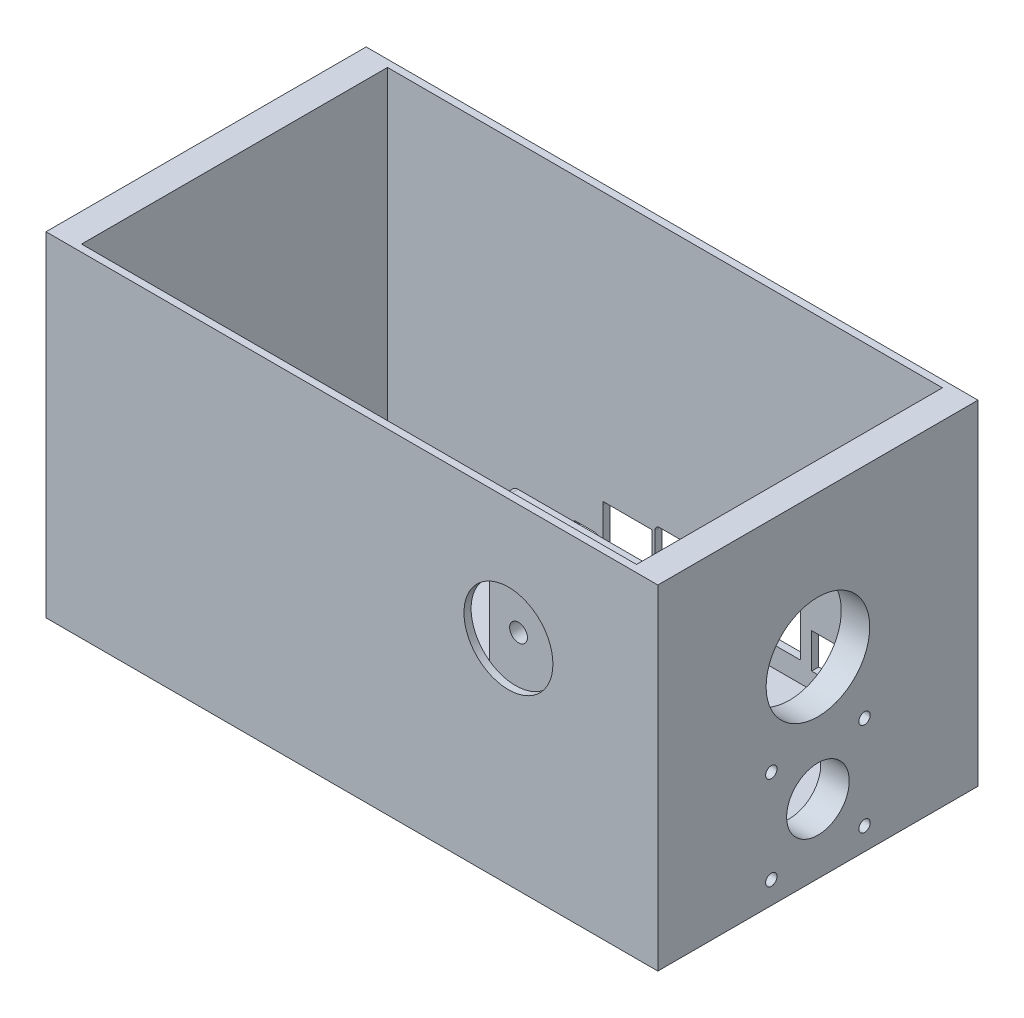
SolidWorks part; units mm, degrees
ref_plane "Front Plane" through (0, 0, 0) normal (0, 0, 1) x (1, 0, 0)
ref_plane "Top Plane" through (0, 0, 0) normal (0, 1, 0) x (1, 0, 0)
ref_plane "Right Plane" through (0, 0, 0) normal (1, 0, 0) x (0, 0, -1)
sketch "Sketch1" plane through (0, 0, 0) normal (0, 1, 0) x (1, 0, 0)
  line L1 (-101.6, -57.15) -> (101.6, -57.15)
  line L2 (-101.6, -57.15) -> (-101.6, 57.15)
  line L3 (-101.6, 57.15) -> (101.6, 57.15)
  line L4 (101.6, -57.15) -> (101.6, 57.15)
  line L5 (-101.6, -57.15) -> (101.6, 57.15) construction
  line L6 (-101.6, 57.15) -> (101.6, -57.15) construction
  point P0 (0, 0)
  dimension "10" = 203.2
  dimension "D2" = 114.3
extrude "Boss-Extrude1" add sketch "Sketch1" along normal blind 119.38
shell "Shell1" thickness 2.54
sketch "Sketch2" plane through (99.06, 0, 0) normal (-1, 0, 0) x (0, 0, 1)
  line L0 (22.225, 46.863) -> (-22.225, 46.863) construction
  line L5 (-22.225, 46.863) -> (-22.225, 2.413) construction
  line L10 (-22.225, 2.413) -> (22.225, 46.863) construction
  line L11 (-22.225, 46.863) -> (22.225, 2.413) construction
  line L12 (22.225, 46.863) -> (22.225, 2.413) construction
  line L14 (22.225, 2.413) -> (-22.225, 2.413) construction
  line L16 (0, 17.0459) -> (0, 33.3047) construction
  line L17 (1.822, 24.638) -> (-4.4847, 24.638) construction
  circle A0 centre (0, 68.58) radius 18.5
  circle A1 centre (16.637, 41.275) radius 2.032
  circle A5 centre (16.637, 8.001) radius 2.032
  circle A6 centre (-16.637, 8.001) radius 2.032
  circle A7 centre (-16.637, 41.275) radius 2.032
  circle A8 centre (0, 24.638) radius 11.176
  point P4 (0, 24.638)
  dimension "D3" = 37
  dimension "D4" = 4.064
  dimension "D5" = 33.274
  dimension "D6" = 22.352
  dimension "D1" = 44.45
  dimension "D2" = 44.45
extrude "Cut-Extrude1" cut sketch "Sketch2" against normal blind 2.54
sketch "Sketch3" plane through (101.6, 0, 0) normal (1, 0, 0) x (0, 0, -1)
  line L4 (-57.15, 0) -> (57.15, 0)
  line L5 (57.15, 0) -> (57.15, 119.38)
  line L6 (57.15, 119.38) -> (-57.15, 119.38)
  line L7 (-57.15, 119.38) -> (-57.15, 0)
  line L8 (-57.15, 0) -> (57.15, 0)
  line L9 (57.15, 0) -> (57.15, 119.38)
  line L10 (57.15, 119.38) -> (-57.15, 119.38)
  line L11 (-57.15, 119.38) -> (-57.15, 0)
  circle A0 centre (0, 68.58) radius 18.5 construction
  circle A1 centre (0, 68.58) radius 18.5
  circle A2 centre (-16.637, 8.001) radius 2.032 construction
  circle A3 centre (16.637, 8.001) radius 2.032 construction
  circle A4 centre (16.637, 41.275) radius 2.032 construction
  circle A5 centre (-16.637, 41.275) radius 2.032 construction
  circle A6 centre (-16.637, 8.001) radius 2.032
  circle A7 centre (16.637, 8.001) radius 2.032
  circle A8 centre (16.637, 41.275) radius 2.032
  circle A9 centre (-16.637, 41.275) radius 2.032
  circle A10 centre (0, 24.638) radius 11.176 construction
  circle A11 centre (0, 24.638) radius 11.176
  dimension "D1" = 0
extrude "Boss-Extrude3" add sketch "Sketch3" along normal blind 7.62
sketch "Sketch4" plane through (0, 0, 57.15) normal (0, 0, 1) x (1, 0, 0)
  line L1 (-101.6, 0) -> (109.22, 0) construction
  line L2 (109.22, 119.38) -> (109.22, 0) construction
  circle A0 centre (55.88, 76.2) radius 15.875
  dimension "D1" = 31.75
  dimension "D2" = 53.34
  dimension "D3" = 76.2
sketch "Sketch5" plane through (0, 2.54, 0) normal (0, 1, 0) x (1, 0, 0)
  line L5 (30.53, -38.55) -> (81.23, -38.55)
  line L6 (30.53, -38.55) -> (30.53, -30.93)
  line L7 (30.53, -30.93) -> (81.23, -30.93)
  line L8 (81.23, -38.55) -> (81.23, -30.93)
  line L9 (74.88, -38.55) -> (74.88, -39.95) construction
  dimension "D1" = 7.62
  dimension "D2" = 6.35
  dimension "D3" = 6.35
extrude "Cut-Extrude2" cut sketch "Sketch4" against normal blind 2.54
extrude "Boss-Extrude4" add sketch "Sketch5" along normal blind 95.25
sketch "Sketch6" plane through (0, 0, 38.55) normal (0, 0, 1) x (1, 0, 0)
  circle A1 centre (40.88, 91.2) radius 3.175
  circle A3 centre (70.88, 61.2) radius 3.175
  circle A4 centre (40.88, 61.2) radius 3.175
  circle A7 centre (70.88, 91.2) radius 3.175
  dimension "D1" = 6.35
  dimension "D2" = 6.35
  dimension "D3" = 6.35
  dimension "D4" = 6.35
extrude "Cut-Extrude3" cut sketch "Sketch6" against normal up to next
fillet "Fillet1" radius 2.54 2 edges at (30.53, 97.79, 34.74) (81.23, 97.79, 34.74)
fillet "Fillet2" radius 2.54 4 edges at (55.88, 2.54, 38.55) (81.23, 2.54, 34.74) (30.53, 2.54, 34.74) (55.88, 2.54, 30.93)
sketch "Sketch7" plane through (-101.6, 0, 0) normal (-1, 0, 0) x (0, 0, 1)
  line L4 (-57.15, 0) -> (57.15, 0)
  line L5 (57.15, 0) -> (57.15, 119.38)
  line L6 (57.15, 119.38) -> (-57.15, 119.38)
  line L7 (-57.15, 119.38) -> (-57.15, 0)
  line L8 (-57.15, 0) -> (57.15, 0)
  line L9 (57.15, 0) -> (57.15, 119.38)
  line L10 (57.15, 119.38) -> (-57.15, 119.38)
  line L11 (-57.15, 119.38) -> (-57.15, 0)
  dimension "D1" = 0
extrude "Boss-Extrude5" add sketch "Sketch7" along normal blind 7.62
sketch "Sketch8" plane through (0, 2.54, 0) normal (0, 1, 0) x (1, 0, 0)
  circle A2 centre (57.7271, -23.7315) radius 2.54
  circle A3 centre (59.6171, 34.2332) radius 2.54
  circle A4 centre (-26.2779, 34.2332) radius 2.54
  circle A5 centre (-28.2729, -23.7315) radius 2.54
  circle A6 centre (57.7271, -23.7315) radius 1.27
  circle A7 centre (59.6171, 34.2332) radius 1.27
  circle A8 centre (-26.2779, 34.2332) radius 1.27
  circle A9 centre (-28.2729, -23.7315) radius 1.27
  dimension "D1" = 5.08
  dimension "D2" = 5.08
  dimension "D3" = 5.08
  dimension "D4" = 5.08
  dimension "D5" = 2.54
  dimension "D6" = 2.54
  dimension "D7" = 2.54
  dimension "D8" = 2.54
extrude "Boss-Extrude6" add sketch "Sketch8" along normal blind 5.08
sketch "Sketch9" plane through (0, 0, -57.15) normal (0, 0, -1) x (-1, 0, 0)
  line L0 (-61.8671, 9.445) -> (-53.3671, 9.445) construction
  line L5 (-53.3671, 9.445) -> (-53.3671, 19.945) construction
  line L6 (-53.3671, 19.945) -> (-61.8671, 19.945) construction
  line L7 (-61.8671, 19.945) -> (-61.8671, 9.445) construction
  line L8 (-61.8671, 9.445) -> (-53.3671, 9.445) construction
  line L9 (-53.3671, 9.445) -> (-53.3671, 19.945) construction
  line L10 (-53.3671, 19.945) -> (-61.8671, 19.945) construction
  line L11 (-61.8671, 19.945) -> (-61.8671, 9.445) construction
  line L12 (-47.5171, 27.3712) -> (-32.2171, 27.3712)
  line L13 (-27.5671, 24.065) -> (-27.5671, 11.045) construction
  line L14 (-26.9671, 24.665) -> (-15.0671, 24.665) construction
  line L15 (-14.4671, 24.065) -> (-14.4671, 11.045) construction
  line L16 (-15.0671, 10.445) -> (-26.9671, 10.445) construction
  line L17 (-9.9671, 24.665) -> (1.9329, 24.665) construction
  line L18 (2.5329, 24.065) -> (2.5329, 11.045) construction
  line L19 (1.9329, 10.445) -> (-9.9671, 10.445) construction
  line L20 (-10.5671, 11.045) -> (-10.5671, 24.065) construction
  line L21 (-48.3171, 26.5712) -> (-48.3171, 10.1681)
  line L22 (-31.4234, 26.6712) -> (-31.4234, 10.107)
  line L23 (-48.0171, 9.8681) -> (-31.7171, 9.8681) construction
  line L24 (-48.0171, 9.8681) -> (-31.7171, 9.8681)
  line L25 (10.7029, 9.545) -> (15.7629, 9.545) construction
  line L26 (-62.8831, 8.429) -> (-52.3511, 8.429)
  line L27 (-52.3511, 8.429) -> (-52.3511, 20.961)
  line L28 (28.3629, 9.3212) -> (28.3629, 9.4912)
  line L29 (28.3629, 9.4912) -> (25.745, 9.4912)
  line L30 (25.5824, 9.5586) -> (24.9202, 10.2207)
  line L31 (24.8529, 10.3833) -> (24.8529, 11.2712)
  line L32 (25.0829, 11.5012) -> (31.6829, 11.5012)
  line L33 (31.9129, 11.2712) -> (31.9128, 10.3833)
  line L34 (31.8455, 10.2207) -> (31.1834, 9.5586)
  line L35 (31.0207, 9.4912) -> (28.4029, 9.4912)
  line L36 (28.4029, 9.4912) -> (28.4029, 9.3212)
  line L37 (28.4029, 9.3212) -> (31.0207, 9.3212)
  line L38 (31.3036, 9.4384) -> (31.9657, 10.1005)
  line L39 (32.0829, 10.3833) -> (32.0829, 11.2712)
  line L40 (31.6829, 11.6712) -> (25.0829, 11.6712)
  line L41 (24.6829, 11.2712) -> (24.6829, 10.3833)
  line L42 (24.8, 10.1005) -> (25.4621, 9.4384)
  line L43 (25.745, 9.3212) -> (28.3629, 9.3212)
  line L53 (28.4029, 9.3212) -> (31.0207, 9.3212) construction
  line L54 (31.3036, 9.4384) -> (31.9657, 10.1005) construction
  line L55 (32.0829, 10.3833) -> (32.0829, 11.2712) construction
  line L56 (31.6829, 11.6712) -> (25.0829, 11.6712) construction
  line L57 (24.6829, 11.2712) -> (24.6829, 10.3833) construction
  line L58 (24.8, 10.1005) -> (25.4621, 9.4384) construction
  line L59 (25.745, 9.3212) -> (28.3629, 9.3212) construction
  line L60 (-52.3511, 20.961) -> (-62.8831, 20.961)
  line L61 (-62.8831, 20.961) -> (-62.8831, 8.429)
  line L62 (28.3629, 8.3052) -> (28.4029, 8.3052)
  line L63 (28.3629, 9.3212) -> (28.4029, 9.3212) construction
  line L66 (-28.5831, 24.065) -> (-28.5831, 11.045)
  line L67 (-15.0671, 9.429) -> (-26.9671, 9.429)
  line L68 (6.7829, 12.5952) -> (6.7829, 14.885)
  line L69 (6.7829, 14.885) -> (6.7829, 16.885)
  line L70 (6.7829, 16.885) -> (6.7829, 20.265)
  line L71 (7.0328, 20.515) -> (19.4329, 20.515)
  line L72 (19.6828, 20.265) -> (19.6829, 16.885)
  line L73 (19.6829, 16.885) -> (19.6829, 14.8862)
  line L74 (19.6829, 14.8862) -> (19.6829, 12.5952)
  line L75 (19.6661, 12.505) -> (20.3829, 12.505)
  line L76 (20.3829, 12.505) -> (20.3829, 10.155)
  line L77 (20.3829, 10.155) -> (15.7629, 10.155)
  line L78 (15.7629, 10.155) -> (15.7629, 9.545)
  line L79 (15.7629, 9.545) -> (20.3329, 9.545)
  line L80 (20.3329, 9.545) -> (21.0828, 9.545)
  line L81 (21.0828, 9.545) -> (21.0829, 22.595)
  line L82 (21.0829, 22.595) -> (21.0829, 22.645)
  line L83 (21.0829, 22.645) -> (5.5829, 22.645)
  line L84 (5.5829, 22.645) -> (5.5829, 22.595)
  line L85 (5.5829, 22.595) -> (5.5829, 9.545)
  line L86 (5.5829, 9.545) -> (6.3329, 9.545)
  line L87 (6.3329, 9.545) -> (10.7029, 9.545)
  line L88 (10.7029, 9.545) -> (10.7029, 10.155)
  line L89 (10.7029, 10.155) -> (6.1829, 10.155)
  line L90 (6.1829, 10.155) -> (6.1829, 12.505)
  line L91 (6.1829, 12.505) -> (6.7996, 12.505)
  line L103 (15.7629, 9.545) -> (20.3329, 9.545) construction
  line L104 (20.3329, 9.545) -> (21.0828, 9.545) construction
  line L105 (21.0828, 9.545) -> (21.0829, 22.595) construction
  line L106 (21.0829, 22.595) -> (21.0829, 22.645) construction
  line L107 (21.0829, 22.645) -> (5.5829, 22.645) construction
  line L108 (5.5829, 22.645) -> (5.5829, 22.595) construction
  line L109 (5.5829, 22.595) -> (5.5829, 9.545) construction
  line L110 (5.5829, 9.545) -> (6.3329, 9.545) construction
  line L111 (6.3329, 9.545) -> (10.7029, 9.545) construction
  line L116 (-13.4511, 24.065) -> (-13.4511, 11.045)
  line L117 (-26.9671, 25.681) -> (-15.0671, 25.681)
  line L118 (-9.9671, 25.681) -> (1.9329, 25.681)
  line L119 (3.5489, 24.065) -> (3.5489, 11.045)
  line L120 (1.9329, 9.429) -> (-9.9671, 9.429)
  line L121 (-11.5831, 11.045) -> (-11.5831, 24.065)
  line L122 (10.7029, 8.529) -> (15.7629, 8.529)
  line L123 (15.7629, 8.529) -> (20.3329, 8.529)
  line L124 (20.3329, 8.529) -> (22.0988, 8.529)
  line L125 (22.0988, 8.529) -> (22.0989, 22.595)
  line L126 (22.0989, 22.595) -> (22.0989, 23.661)
  line L127 (22.0989, 23.661) -> (4.5669, 23.661)
  line L128 (4.5669, 23.661) -> (4.5669, 22.595)
  line L129 (4.5669, 22.595) -> (4.5669, 8.529)
  line L130 (4.5669, 8.529) -> (6.3329, 8.529)
  line L131 (6.3329, 8.529) -> (10.7029, 8.529)
  line L132 (28.4029, 8.3052) -> (31.0207, 8.3052)
  line L133 (32.022, 8.7199) -> (32.6841, 9.3821)
  line L134 (33.0989, 10.3833) -> (33.0989, 11.2712)
  line L135 (31.6829, 12.6872) -> (25.0829, 12.6872)
  line L136 (23.6669, 11.2712) -> (23.6669, 10.3833)
  line L137 (24.0816, 9.3821) -> (24.7437, 8.7199)
  line L138 (25.745, 8.3052) -> (28.3629, 8.3052)
  line L139 (-47.3011, 26.3552) -> (-32.4394, 26.3552) construction
  line L140 (-47.3011, 26.3552) -> (-47.3011, 10.8841) construction
  line L141 (-32.4394, 26.3552) -> (-32.4394, 10.107) construction
  line L142 (-47.3011, 10.8841) -> (-32.138, 10.8841) construction
  arc A1 (-47.5171, 27.3712) -> (-48.3171, 26.5712) centre (-47.5171, 26.5712) ccw construction
  arc A2 (6.7829, 12.5952) -> (6.7996, 12.505) centre (7.0337, 12.5952) ccw
  arc A3 (7.0328, 20.515) -> (6.7829, 20.265) centre (7.0328, 20.265) ccw
  arc A4 (19.6828, 20.265) -> (19.4329, 20.515) centre (19.4329, 20.265) ccw
  arc A5 (19.6661, 12.505) -> (19.6829, 12.5952) centre (19.432, 12.5952) ccw
  arc A10 (-31.4234, 26.6712) -> (-32.2171, 27.3712) centre (-32.2171, 26.5712) ccw construction
  arc A11 (-26.9671, 24.665) -> (-27.5671, 24.065) centre (-26.9671, 24.065) ccw construction
  arc A12 (25.5824, 9.5586) -> (25.745, 9.4912) centre (25.745, 9.7212) ccw
  arc A13 (24.8529, 10.3833) -> (24.9202, 10.2207) centre (25.0829, 10.3833) ccw
  arc A14 (25.0829, 11.5012) -> (24.8529, 11.2712) centre (25.0829, 11.2712) ccw
  arc A15 (31.9129, 11.2712) -> (31.6829, 11.5012) centre (31.6829, 11.2712) ccw
  arc A16 (31.8455, 10.2207) -> (31.9128, 10.3833) centre (31.6829, 10.3833) ccw
  arc A17 (31.0207, 9.4912) -> (31.1834, 9.5586) centre (31.0207, 9.7212) ccw
  arc A18 (31.0207, 9.3212) -> (31.3036, 9.4384) centre (31.0207, 9.7212) ccw
  arc A19 (31.9657, 10.1005) -> (32.0829, 10.3833) centre (31.6829, 10.3833) ccw
  arc A20 (32.0829, 11.2712) -> (31.6829, 11.6712) centre (31.6829, 11.2712) ccw
  arc A21 (25.0829, 11.6712) -> (24.6829, 11.2712) centre (25.0829, 11.2712) ccw
  arc A22 (24.6829, 10.3833) -> (24.8, 10.1005) centre (25.0829, 10.3833) ccw
  arc A23 (25.4621, 9.4384) -> (25.745, 9.3212) centre (25.745, 9.7212) ccw
  arc A30 (31.0207, 9.3212) -> (31.3036, 9.4384) centre (31.0207, 9.7212) ccw construction
  arc A31 (31.9657, 10.1005) -> (32.0829, 10.3833) centre (31.6829, 10.3833) ccw construction
  arc A32 (32.0829, 11.2712) -> (31.6829, 11.6712) centre (31.6829, 11.2712) ccw construction
  arc A33 (25.0829, 11.6712) -> (24.6829, 11.2712) centre (25.0829, 11.2712) ccw construction
  arc A34 (24.6829, 10.3833) -> (24.8, 10.1005) centre (25.0829, 10.3833) ccw construction
  arc A35 (25.4621, 9.4384) -> (25.745, 9.3212) centre (25.745, 9.7212) ccw construction
  arc A36 (-27.5671, 11.045) -> (-26.9671, 10.445) centre (-26.9671, 11.045) ccw construction
  arc A37 (-15.0671, 10.445) -> (-14.4671, 11.045) centre (-15.0671, 11.045) ccw construction
  arc A38 (-10.5671, 11.045) -> (-9.9671, 10.445) centre (-9.9671, 11.045) ccw construction
  arc A39 (1.9329, 10.445) -> (2.5329, 11.045) centre (1.9329, 11.045) ccw construction
  arc A40 (2.5329, 24.065) -> (1.9329, 24.665) centre (1.9329, 24.065) ccw construction
  arc A41 (-9.9671, 24.665) -> (-10.5671, 24.065) centre (-9.9671, 24.065) ccw construction
  arc A42 (-14.4671, 24.065) -> (-15.0671, 24.665) centre (-15.0671, 24.065) ccw construction
  arc A43 (-48.3171, 10.1681) -> (-48.0171, 9.8681) centre (-48.0171, 10.1681) ccw construction
  arc A44 (-47.5171, 27.3712) -> (-48.3171, 26.5712) centre (-47.5171, 26.5712) ccw
  arc A45 (-31.4234, 26.6712) -> (-32.2171, 27.3712) centre (-32.2171, 26.5712) ccw
  arc A46 (-26.9671, 24.665) -> (-27.5671, 24.065) centre (-26.9671, 24.065) ccw construction
  arc A47 (-27.5671, 11.045) -> (-26.9671, 10.445) centre (-26.9671, 11.045) ccw construction
  arc A48 (-15.0671, 10.445) -> (-14.4671, 11.045) centre (-15.0671, 11.045) ccw construction
  arc A49 (-10.5671, 11.045) -> (-9.9671, 10.445) centre (-9.9671, 11.045) ccw construction
  arc A50 (1.9329, 10.445) -> (2.5329, 11.045) centre (1.9329, 11.045) ccw construction
  arc A51 (2.5329, 24.065) -> (1.9329, 24.665) centre (1.9329, 24.065) ccw construction
  arc A52 (-9.9671, 24.665) -> (-10.5671, 24.065) centre (-9.9671, 24.065) ccw construction
  arc A53 (-14.4671, 24.065) -> (-15.0671, 24.665) centre (-15.0671, 24.065) ccw construction
  arc A54 (-48.3171, 10.1681) -> (-48.0171, 9.8681) centre (-48.0171, 10.1681) ccw
  arc A55 (-31.7171, 9.8681) -> (-31.4171, 10.1681) centre (-31.7171, 10.1681) ccw construction
  arc A56 (-31.7171, 9.8681) -> (-31.4171, 10.1681) centre (-31.7171, 10.1681) ccw
  arc A57 (-32.138, 10.8841) -> (-32.138, 10.8841) centre (-32.138, 10.8841) cw
  arc A58 (-47.3011, 10.8841) -> (-47.3011, 10.8841) centre (-47.3011, 10.8841) ccw
  arc A59 (-47.3011, 26.3552) -> (-47.3011, 26.3552) centre (-47.3011, 26.3552) ccw
  arc A60 (-32.4394, 26.3552) -> (-32.4394, 26.3552) centre (-32.4394, 26.3552) ccw
  arc A61 (-28.5831, 11.045) -> (-26.9671, 9.429) centre (-26.9671, 11.045) ccw
  arc A62 (-15.0671, 9.429) -> (-13.4511, 11.045) centre (-15.0671, 11.045) ccw
  arc A63 (-13.4511, 24.065) -> (-15.0671, 25.681) centre (-15.0671, 24.065) ccw
  arc A64 (-26.9671, 25.681) -> (-28.5831, 24.065) centre (-26.9671, 24.065) ccw
  arc A65 (3.5489, 24.065) -> (1.9329, 25.681) centre (1.9329, 24.065) ccw
  arc A66 (1.9329, 9.429) -> (3.5489, 11.045) centre (1.9329, 11.045) ccw
  arc A67 (-11.5831, 11.045) -> (-9.9671, 9.429) centre (-9.9671, 11.045) ccw
  arc A68 (-9.9671, 25.681) -> (-11.5831, 24.065) centre (-9.9671, 24.065) ccw
  arc A69 (31.0207, 8.3052) -> (32.022, 8.7199) centre (31.0207, 9.7212) ccw
  arc A70 (32.6841, 9.3821) -> (33.0989, 10.3833) centre (31.6829, 10.3833) ccw
  arc A71 (33.0989, 11.2712) -> (31.6829, 12.6872) centre (31.6829, 11.2712) ccw
  arc A72 (25.0829, 12.6872) -> (23.6669, 11.2712) centre (25.0829, 11.2712) ccw
  arc A73 (23.6669, 10.3833) -> (24.0816, 9.3821) centre (25.0829, 10.3833) ccw
  arc A74 (24.7437, 8.7199) -> (25.745, 8.3052) centre (25.745, 9.7212) ccw
  dimension "D1" = 0
  dimension "D2" = 0
  dimension "D3" = 1.016
extrude "Cut-Extrude5" cut sketch "Sketch9" against normal blind 2.54 contours L60 L61 L26 L27 | L137 A74 L138 L62 L132 A69 L133 A70 L134 A71 L135 A72 L136 A73 | L130 L131 L122 L123 L124 L125 L126 L127 L128 L129 | L118 A68 L121 A67 L120 A66 L119 A65 | L117 A64 L66 A61 L67 A62 L116 A63 | L24 A56 L22 A45 L12 A44 L21 A54
